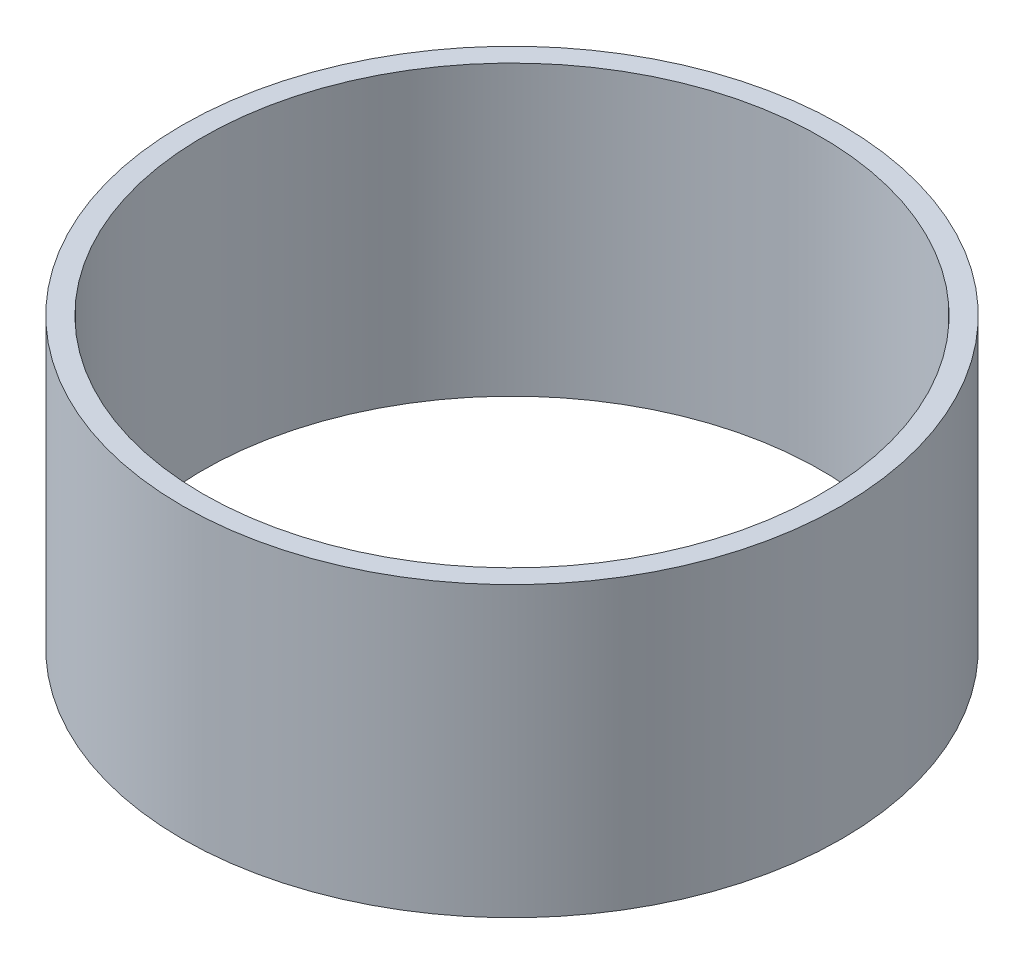
SolidWorks part; units mm, degrees
ref_plane "Front Plane" through (0, 0, 0) normal (0, 0, 1) x (1, 0, 0)
ref_plane "Top Plane" through (0, 0, 0) normal (0, 1, 0) x (1, 0, 0)
ref_plane "Right Plane" through (0, 0, 0) normal (1, 0, 0) x (0, 0, -1)
sketch "Sketch1" plane through (0, 0, 0) normal (0, 1, 0) x (1, 0, 0)
  circle A0 centre (0, 0) radius 30
  dimension "D1" = 60
extrude "Extrude-Thin1" add sketch "Sketch1" along normal blind 28 thin
